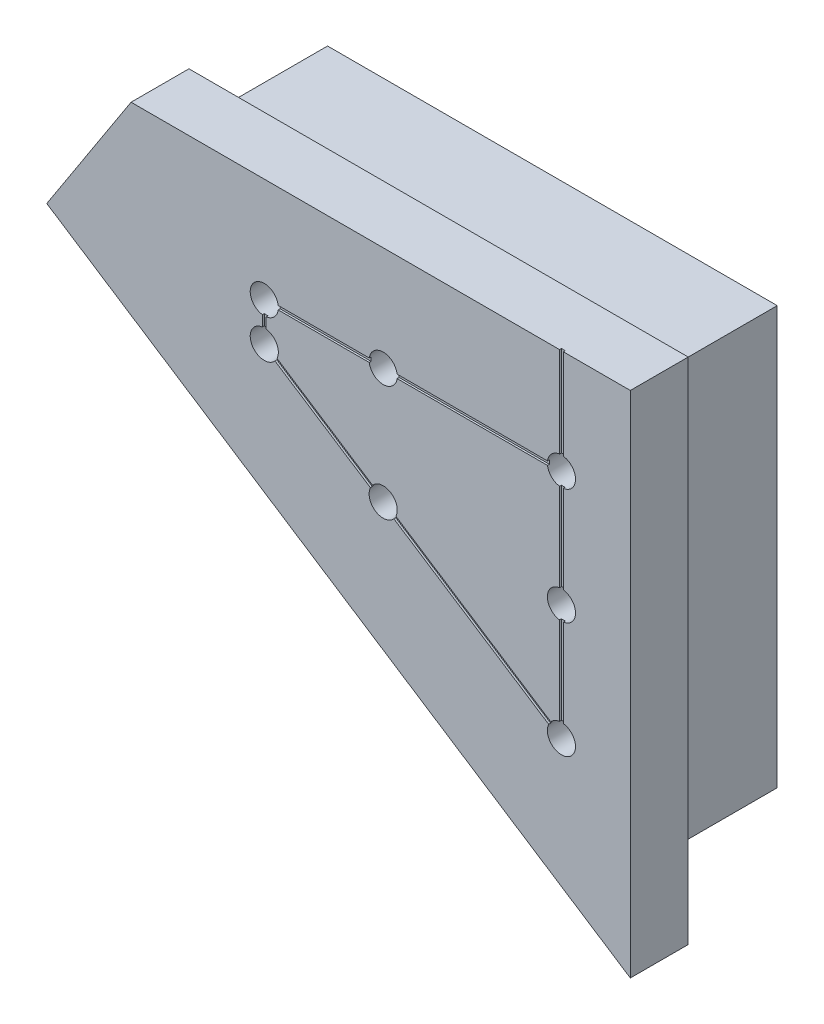
SolidWorks part; units mm, degrees
material "6061-T6 Al"
ref_plane "Front" through (0, 0, 0) normal (0, 0, 1) x (1, 0, 0)
ref_plane "Top" through (0, 0, 0) normal (0, 1, 0) x (1, 0, 0)
ref_plane "Right" through (0, 0, 0) normal (1, 0, 0) x (0, 0, -1)
sketch "Sketch1" plane through (0, 0, 0) normal (0, 0, 1) x (1, 0, 0)
  line L0 (-177.8, 0) -> (-200.4721, -34.9119)
  line L1 (-177.8, 0) -> (0, 0)
  line L2 (0, -165.1) -> (-200.4721, -34.9119)
  line L5 (0, 0) -> (0, -165.1)
  line L14 (55, 0) -> (-55, 0) construction
  point P8 (0.4623, -190.789)
  dimension "D1" = 177.8
  dimension "D3" = 57
  dimension "D7" = 165.1
extrude "Boss-Extrude1" add sketch "Sketch1" along normal blind 70.7898
hole_wizard "CBORE for #10 Socket Head Cap Screw1" positions "Sketch12" profile "Sketch11" counterbore size "#10" standard "Ansi Inch" end condition through all
sketch "Sketch12" plane through (0, 0, 70.7898) normal (0, 0, 1) x (1, 0, 0)
  line L12 (-132.0317, -28.575) -> (-132.0317, -43.8224) construction
  line L13 (0, 0) -> (-177.8, 0) construction
  line L14 (0, -165.1) -> (0, 0) construction
  line L15 (-14.5358, -28.575) -> (-85.0232, -28.575) construction
  line L16 (-85.0232, -74.3501) -> (-14.5358, -74.3501) construction
  line L17 (-14.5358, -120.1251) -> (-85.0232, -74.3501) construction
  line L18 (-14.5358, -28.575) -> (-14.5358, -74.3501) construction
  line L19 (-14.5358, -74.3501) -> (-14.5358, -120.1251) construction
  line L20 (-85.0232, -28.575) -> (-85.0232, -74.3501) construction
  line L21 (-85.0232, -74.3501) -> (-132.0317, -43.8224) construction
  line L22 (-85.0232, -28.575) -> (-132.0317, -28.575) construction
  point P1 (-132.0317, -28.575)
  point P4 (-14.5358, -28.575)
  point P7 (-14.5358, -74.3501)
  point P10 (-14.5358, -120.1251)
  point P16 (-85.0232, -74.3501)
  point P44 (-85.0232, -28.575)
  point P114 (-132.0317, -43.8224)
other "AlignGroup4" parameters "D1"=0, "D2"=28.2683, "D3"=62.9338, "D4"=69.4625, "D5"=126.4336, "D6"=133.4695, "D7"=168.0098, "D8"=0, "D9"=31.71, "D10"=55.271, "D11"=38.3146, "D12"=66.6881, "D13"=106.0707, "D14"=108.0344
sketch "Sketch11" plane through (-132.0317, -28.575, 70.7898) normal (1, 0, 0) x (0, -1, 0)
  line L0 (0, 0) -> (0, 70.7898)
  line L1 (0, 70.7898) -> (2.7686, 70.7898)
  line L3 (2.7686, 70.7898) -> (2.7686, 66.8274)
  line L4 (2.7686, 66.8274) -> (5.5626, 66.8274)
  line L5 (5.5626, 66.8274) -> (5.5626, 0)
  line L7 (5.5626, 0) -> (0, 0)
  line L11 (0, -6.35) -> (0, 107.95) construction
  dimension "Thru Hole Dia." = 5.5372
  dimension "Thru Hole Depth" = 70.7898
  dimension "C'Bore Dia." = 11.1252
  dimension "C'Bore Depth" = 66.8274
sketch "Sketch13" plane through (0, 0, 70.7898) normal (0, 0, 1) x (1, 0, 0)
  line L0 (0, -165.1) -> (0, 0)
  line L1 (0, 0) -> (-177.8, 0)
  line L2 (-177.8, 0) -> (-200.4721, -34.9119)
  line L3 (-200.4721, -34.9119) -> (0, -165.1)
  line L4 (12.7, 12.7) -> (-184.6955, 12.7)
  line L5 (-184.6955, 12.7) -> (-218.0401, -38.6461)
  line L6 (-218.0401, -38.6461) -> (12.7, -188.4905)
  line L7 (12.7, -188.4905) -> (12.7, 12.7)
  dimension "D1" = 12.7
extrude "Boss-Extrude2" add sketch "Sketch13" against normal blind 22.8854
fillet "Fillet2" radius 2.3368 4 edges at (0, -82.55, 47.9044) (-100.236, -100.006, 47.9044) (-189.136, -17.456, 47.9044) (-88.9, 0, 47.9044)
sketch "Sketch14" plane through (0, 0, 70.7898) normal (0, 0, 1) x (1, 0, 0)
  line L0 (-14.5358, -120.1251) -> (-132.0317, -43.8224) construction
  line L1 (-132.0317, -43.8224) -> (-132.0317, -28.575) construction
  line L2 (-132.0317, -28.575) -> (-14.5358, -28.575) construction
  line L3 (-14.5358, -120.1251) -> (-14.5358, -28.575) construction
  line L4 (-14.9508, -120.7642) -> (-132.4467, -44.4614)
  line L5 (-132.7937, -43.8224) -> (-132.7937, -28.575)
  line L6 (-132.0317, -27.813) -> (-15.2978, -27.813)
  line L7 (-13.7738, -120.1251) -> (-13.7738, 12.7)
  line L8 (-16.4748, -117.9573) -> (-130.9227, -43.634)
  line L9 (-131.2697, -42.9949) -> (-131.2697, -30.099)
  line L10 (-130.5077, -29.337) -> (-15.2978, -29.337)
  line L11 (-15.2978, -117.3183) -> (-15.2978, -29.337)
  line L12 (-13.7738, 12.7) -> (-15.2978, 12.7)
  line L14 (-13.7738, -120.1251) -> (-13.7738, -28.575) construction
  line L15 (-15.2978, -120.1251) -> (-15.2978, -28.575) construction
  line L16 (-15.2978, -27.813) -> (-15.2978, 12.7)
  line L17 (-132.0317, -27.813) -> (-14.5358, -27.813) construction
  line L18 (-132.0317, -29.337) -> (-14.5358, -29.337) construction
  line L19 (-14.9508, -120.7642) -> (-132.4467, -44.4614) construction
  line L20 (-14.1208, -119.4861) -> (-131.6167, -43.1833) construction
  line L21 (-132.7937, -43.8224) -> (-132.7937, -28.575) construction
  line L22 (-131.2697, -43.8224) -> (-131.2697, -28.575) construction
  line L23 (12.7, 12.7) -> (-184.6955, 12.7) construction
  arc A0 (-13.7738, -120.1251) -> (-14.9508, -120.7642) centre (-14.5358, -120.1251) cw
  arc A1 (-15.2978, -117.3183) -> (-16.4748, -117.9573) centre (-16.0598, -117.3183) cw
  arc A2 (-132.0317, -27.813) -> (-132.7937, -28.575) centre (-132.0317, -28.575) ccw
  arc A3 (-130.5077, -29.337) -> (-131.2697, -30.099) centre (-130.5077, -30.099) ccw
  arc A4 (-132.4467, -44.4614) -> (-132.7937, -43.8224) centre (-132.0317, -43.8224) cw
  arc A5 (-130.9227, -43.634) -> (-131.2697, -42.9949) centre (-130.5077, -42.9949) cw
  dimension "D9" = 0.762
  dimension "D10" = 0.762
  dimension "D1" = 0.762
  dimension "D2" = 0.762
  dimension "D3" = 0.762
  dimension "D4" = 0.762
  dimension "D5" = 0.762
  dimension "D6" = 0.762
  dimension "D7" = 0.762
  dimension "D8" = 0.762
extrude "Cut-Extrude1" cut sketch "Sketch14" against normal blind 0.762
